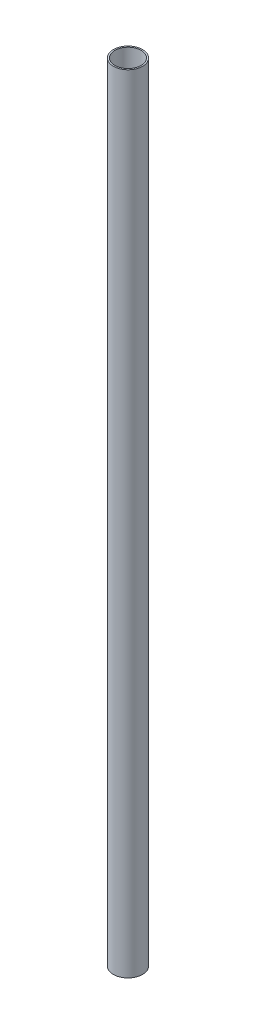
SolidWorks part; units mm, degrees
material "AISI 316 Stainless Steel Sheet (SS)"
ref_plane "Front Plane" through (0, 0, 0) normal (0, 0, 1) x (1, 0, 0)
ref_plane "Top Plane" through (0, 0, 0) normal (0, 1, 0) x (1, 0, 0)
ref_plane "Right Plane" through (0, 0, 0) normal (1, 0, 0) x (0, 0, -1)
sketch "Sketch1" plane through (0, 0, 0) normal (0, 1, 0) x (1, 0, 0)
  circle A0 centre (0, 0) radius 0.5
  circle A1 centre (0, 0) radius 0.45
  dimension "D1" = 0.05
  dimension "D2" = 1
extrude "Boss-Extrude1" add sketch "Sketch1" along normal blind 27
hole_wizard "Ø0.5 (0.5) Diameter Hole1" positions "3DSketch1" profile "Sketch2" hole size "Ø0.5" standard "ISO"
sketch3d "3DSketch1"
  point P0 (-0.0061, 14.81, -0.5)
sketch "Sketch2" plane through (-0.0061, 14.81, -0.5) normal (0, 1, 0) x (-0.9999, 0, 0.0122)
  line L0 (0, 0) -> (0, 0.05)
  line L1 (0, 0.05) -> (0.25, 0.05)
  line L2 (0.25, 0.05) -> (0.25, 0)
  line L5 (0.25, 0) -> (0, 0)
  line L11 (0, -6.35) -> (0, 107.95) construction
  dimension "Thru Hole Dia." = 0.5
  dimension "Thru Hole Depth" = 0.05
